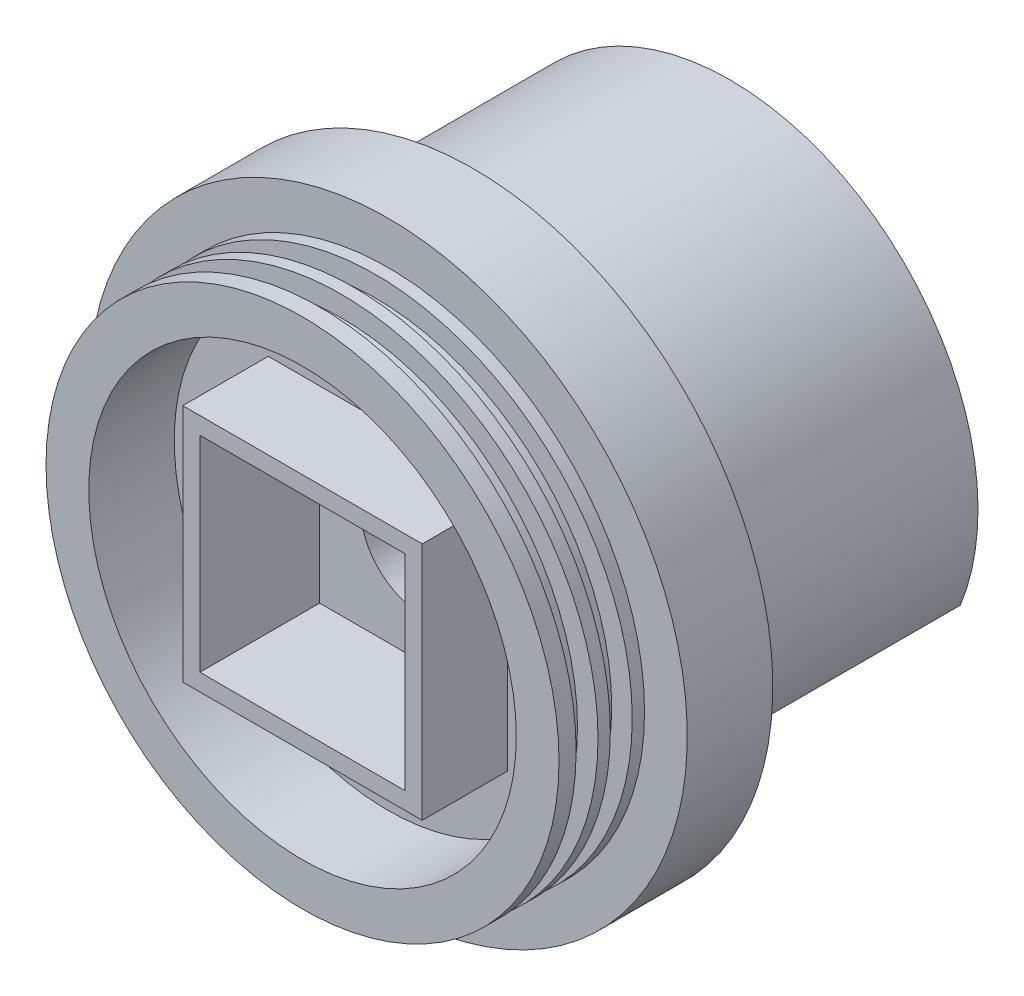
SolidWorks part; units mm, degrees
material "ABS"
ref_plane "Front Plane" through (0, 0, 0) normal (0, 0, 1) x (1, 0, 0)
ref_plane "Top Plane" through (0, 0, 0) normal (0, 1, 0) x (1, 0, 0)
ref_plane "Right Plane" through (0, 0, 0) normal (1, 0, 0) x (0, 0, -1)
sketch "Sketch1" plane through (0, 0, 0) normal (0, 0, 1) x (1, 0, 0)
  circle A0 centre (0, 0) radius 38.1
  dimension "D1" = 76.2
extrude "Boss-Extrude1" add sketch "Sketch1" along normal blind 12.7 contours A0
sketch "Sketch3" plane through (0, 0, 0) normal (0, 0, -1) x (-1, 0, 0)
  circle A0 centre (0, 0) radius 44.45
  dimension "D1" = 88.9
extrude "Boss-Extrude2" add sketch "Sketch3" along normal blind 12.7
sketch "Sketch4" plane through (0, 0, -12.7) normal (0, 0, -1) x (-1, 0, 0)
  circle A0 centre (0, 0) radius 9.144
  dimension "D1" = 18.288
extrude "Cut-Extrude1" cut sketch "Sketch4" against normal through all
sketch "Sketch5" plane through (0, 0, 12.7) normal (0, 0, 1) x (1, 0, 0)
  line L1 (-15.24, 15.24) -> (15.24, 15.24)
  line L2 (-15.24, 15.24) -> (-15.24, -15.24)
  line L3 (-15.24, -15.24) -> (15.24, -15.24)
  line L4 (15.24, 15.24) -> (15.24, -15.24)
  line L5 (-15.24, 15.24) -> (15.24, -15.24) construction
  line L6 (-15.24, -15.24) -> (15.24, 15.24) construction
  point P0 (0, 0)
  dimension "D1" = 30.48
extrude "Cut-Extrude2" cut sketch "Sketch5" against normal blind 17.78
sketch "Sketch6" plane through (0, 0, 12.7) normal (0, 0, 1) x (1, 0, 0)
  circle A0 centre (0, 0) radius 31.75
  dimension "D1" = 63.5
extrude "Cut-Extrude3" cut sketch "Sketch6" against normal blind 12.7
sketch "Sketch7" plane through (0, 0, -12.7) normal (0, 0, -1) x (-1, 0, 0)
  line L0 (-34.2113, -13.6394) -> (-31.4606, -13.6394)
  line L2 (31.4606, -13.6394) -> (34.2113, -13.6394)
  arc A2 (31.4606, -13.6394) -> (-31.4606, -13.6394) centre (0, 0) ccw
  arc A3 (34.2113, -13.6394) -> (-34.2113, -13.6394) centre (0, 0) ccw
  circle A4 centre (0, 0) radius 34.29 construction
  circle A5 centre (0, 0) radius 36.83 construction
  dimension "D1" = 68.58
  dimension "D2" = 2.54
extrude "Boss-Extrude3" add sketch "Sketch7" along normal blind 38.1
sketch "Sketch8" plane through (0, 0, 12.7) normal (0, 0, 1) x (1, 0, 0)
  circle A0 centre (0, 0) radius 38.1
  circle A3 centre (0, 0) radius 35.052
  dimension "D1" = 3.048
extrude "Cut-Extrude4" cut sketch "Sketch8" against normal blind 3.2512 from offset 2.54 offset against normal yes
sketch "Sketch9" plane through (0, 0, 12.7) normal (0, 0, 1) x (1, 0, 0)
  circle A0 centre (0, 0) radius 38.1
  circle A1 centre (0, 0) radius 35.052
  dimension "D1" = 3.048
extrude "Cut-Extrude5" cut sketch "Sketch9" against normal blind 3.2512 from offset 7.62 offset against normal yes
fillet "Fillet1" radius 2.54 4 edges at (0, 34.29, -12.7) (-32.836, -13.6394, -12.7) (32.836, -13.6394, -12.7) (0, 36.83, -12.7)
sketch "Sketch10" plane through (0, 0, 0) normal (0, 0, 1) x (1, 0, 0)
  line L0 (15.24, -15.24) -> (-15.24, -15.24) construction
  line L1 (15.24, 15.24) -> (15.24, -15.24) construction
  line L2 (-15.24, -15.24) -> (-15.24, 15.24) construction
  line L3 (-15.24, 15.24) -> (15.24, 15.24) construction
  line L4 (15.24, -15.24) -> (-15.24, -15.24)
  line L5 (15.24, 15.24) -> (15.24, -15.24)
  line L6 (-15.24, -15.24) -> (-15.24, 15.24)
  line L7 (-15.24, 15.24) -> (15.24, 15.24)
  line L8 (17.78, -17.78) -> (-17.78, -17.78)
  line L9 (-17.78, -17.78) -> (-17.78, 17.78)
  line L10 (-17.78, 17.78) -> (17.78, 17.78)
  line L11 (17.78, 17.78) -> (17.78, -17.78)
  dimension "D1" = 2.54
extrude "Boss-Extrude4" add sketch "Sketch10" along normal blind 12.7
